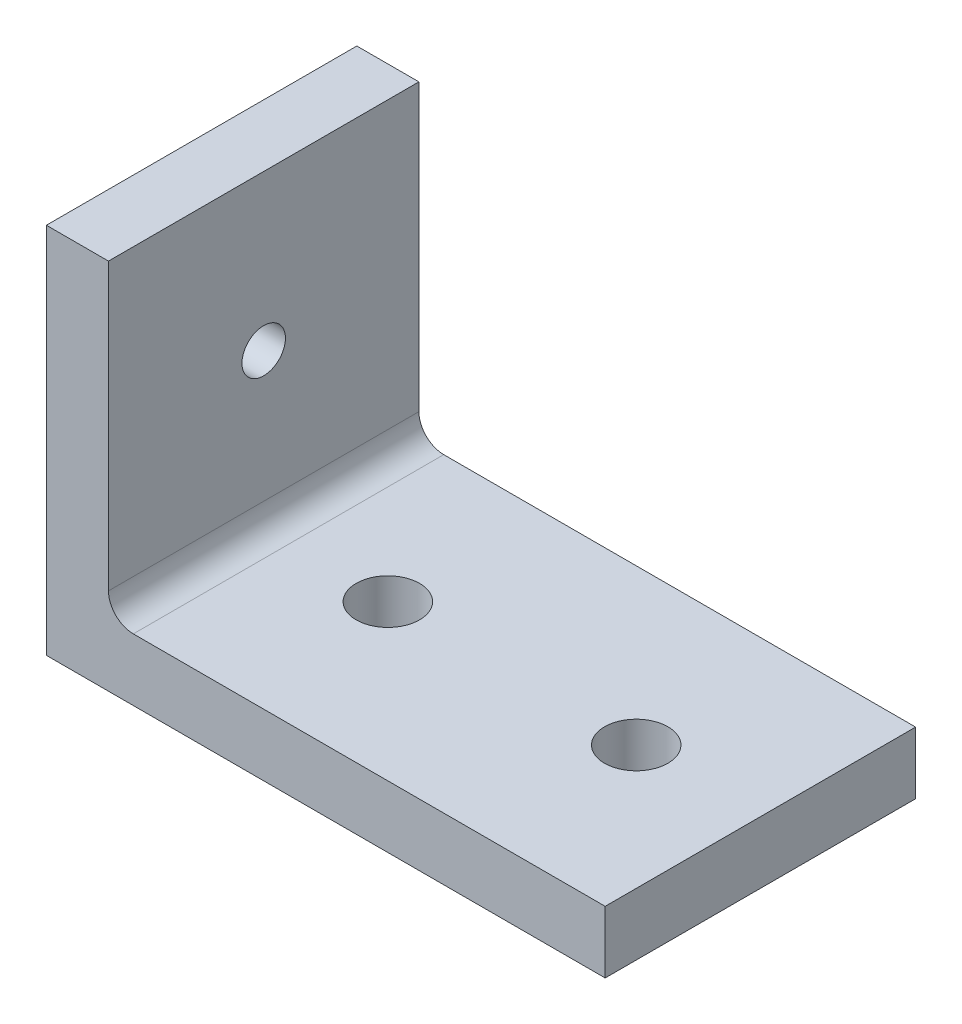
SolidWorks part; units mm, degrees
ref_plane "Front Plane" through (0, 0, 0) normal (0, 0, 1) x (1, 0, 0)
ref_plane "Top Plane" through (0, 0, 0) normal (0, 1, 0) x (1, 0, 0)
ref_plane "Right Plane" through (0, 0, 0) normal (1, 0, 0) x (0, 0, -1)
sketch "Sketch1" plane through (0, 0, 0) normal (0, 0, 1) x (1, 0, 0)
  line L0 (0, 30) -> (0, 0)
  line L1 (0, 0) -> (45, 0) construction
  line L2 (0, 0) -> (0, 5) construction
  line L3 (0, 5) -> (45, 5) construction
  line L4 (45, 0) -> (45, 5) construction
  line L5 (0, 0) -> (5, 0) construction
  line L6 (0, 0) -> (0, 30) construction
  line L7 (0, 30) -> (5, 30) construction
  line L8 (5, 0) -> (5, 30) construction
  line L9 (0, 0) -> (45, 0)
  line L10 (45, 0) -> (45, 5)
  line L11 (45, 5) -> (5, 5)
  line L12 (5, 5) -> (5, 30)
  line L13 (5, 30) -> (0, 30)
  dimension "D1" = 5
  dimension "D2" = 5
  dimension "D3" = 45
  dimension "D4" = 30
extrude "Boss-Extrude1" add sketch "Sketch1" along normal blind 25 contours L12 L13 L0 L9 L10 L11
sketch "Sketch2" plane through (5, 0, 0) normal (1, 0, 0) x (0, 0, -1)
  line L0 (-12.5, 30) -> (-12.5, 5) construction
  line L1 (-25, 30) -> (0, 30) construction
  line L2 (-25, 5) -> (0, 5) construction
  line L3 (-25, 17.5) -> (0, 17.5) construction
  line L4 (-25, 5) -> (-25, 30) construction
  line L5 (0, 5) -> (0, 30) construction
  circle A0 centre (-12.5, 17.5) radius 1.75
  point P14 (0, 0)
  point P15 (0, 0)
  dimension "D1" = 3.5
extrude "Cut-Extrude1" cut sketch "Sketch2" against normal blind 25
fillet "Fillet1" radius 2 1 edges at (5, 5, 12.5)
sketch "Sketch4" plane through (0, 5, 0) normal (0, 1, 0) x (1, 0, 0)
  line L0 (45, -12.5) -> (7, -12.5) construction
  line L1 (45, -25) -> (45, 0) construction
  line L2 (7, 0) -> (7, -25) construction
  circle A0 centre (35, -12.5) radius 2.55
  circle A1 centre (15, -12.5) radius 2.55
  dimension "D1" = 5.1
  dimension "D2" = 5.1
  dimension "D3" = 10
  dimension "D4" = 20
extrude "Cut-Extrude2" cut sketch "Sketch4" against normal blind 25 contours A1
